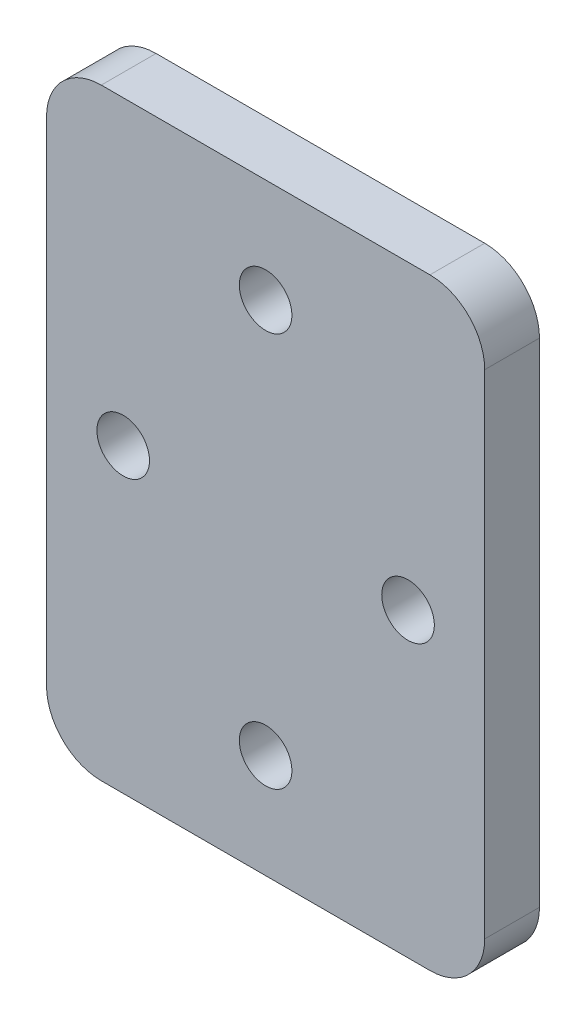
SolidWorks part; units mm, degrees
ref_plane "Front Plane" through (0, 0, 0) normal (0, 0, 1) x (1, 0, 0)
ref_plane "Top Plane" through (0, 0, 0) normal (0, 1, 0) x (1, 0, 0)
ref_plane "Right Plane" through (0, 0, 0) normal (1, 0, 0) x (0, 0, -1)
sketch "Sketch1" plane through (0, 0, 0) normal (0, 0, 1) x (1, 0, 0)
  line L1 (-20, 27.5) -> (20, 27.5)
  line L2 (-20, 27.5) -> (-20, -27.5)
  line L3 (-20, -27.5) -> (20, -27.5)
  line L4 (20, 27.5) -> (20, -27.5)
  line L5 (0, -27.5) -> (0, 27.5) construction
  line L6 (-20, 0) -> (20, 0) construction
  circle A0 centre (0, 18) radius 2.4
  circle A1 centre (-13, 0) radius 2.4
  circle A2 centre (0, -18) radius 2.4
  circle A3 centre (13, 0) radius 2.4
  point P0 (0, 0)
  dimension "D3" = 4.8
  dimension "D5" = 4.8
  dimension "D1" = 55
  dimension "D2" = 40
  dimension "D4" = 18
  dimension "D6" = 13
extrude "Boss-Extrude1" add sketch "Sketch1" along normal blind 5
fillet "Fillet1" radius 5 4 edges at (20, -27.5, 2.5) (-20, -27.5, 2.5) (20, 27.5, 2.5) (-20, 27.5, 2.5)
